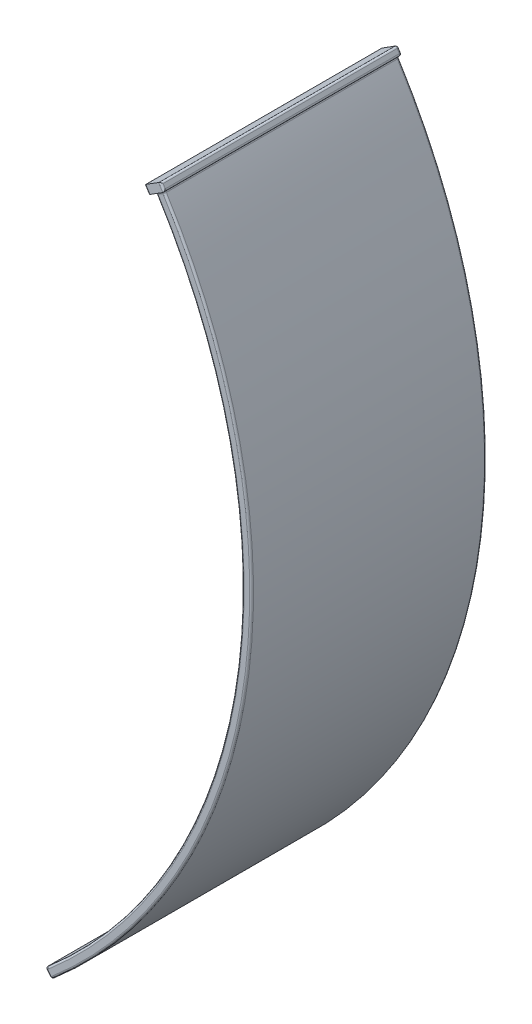
SolidWorks part; units mm, degrees
ref_plane "Front Plane" through (0, 0, 0) normal (0, 0, 1) x (1, 0, 0)
ref_plane "Top Plane" through (0, 0, 0) normal (0, 1, 0) x (1, 0, 0)
ref_plane "Right Plane" through (0, 0, 0) normal (1, 0, 0) x (0, 0, -1)
ref_plane "Plane1" through (-17.5, 0, 0) normal (1, 0, 0) x (0, 0, -1)
ref_plane "Plane2" through (-35, 0, 0) normal (1, 0, 0) x (0, 0, -1)
sketch "Sketch1" plane through (-17.5, 0, 0) normal (1, 0, 0) x (0, 0, -1)
  line L0 (0, 0) -> (0, -50) construction
  dimension "D1" = 50
sketch "Sketch2" plane through (0, 0, 0) normal (1, 0, 0) x (0, 0, -1)
  point P0 (0, 0)
sketch "Sketch3" plane through (-35, 0, 0) normal (1, 0, 0) x (0, 0, -1)
  point P0 (0, 0)
sketch "Sketch4" plane through (0, 0, 0) normal (0, 0, 1) x (1, 0, 0)
  line L0 (-17.5, 0) -> (-17.5, -50) construction
  arc A0 (9.9992, -0.126) -> (-45, -0.1273) centre (-17.5, -17.4818) cw construction
  arc A1 (9.9992, -0.126) -> (3.7287, -42.1146) centre (-17.5, -17.4818) cw construction
  dimension "D1" = 10
  dimension "D3" = 32.5182
  dimension "D4" = 46.2567
  dimension "D2" = 10
sketch "Sketch6" plane through (0, 0, 0) normal (0, 0, 1) x (1, 0, 0)
  line L0 (15.0182, 10) -> (15.0182, -39.6825) construction
  arc A0 (3.7287, -42.1146) -> (9.9992, -0.126) centre (-17.5, -17.4818) ccw construction
  dimension "D1" = 32.5182
ref_plane "Plane3" through (15.0182, 0, 0) normal (1, 0, 0) x (0, 0, -1)
sketch "Sketch7" plane through (0, 0, 0) normal (0, 0, 1) x (1, 0, 0)
  arc A0 (12.8322, 1.6619) -> (5.9157, -44.6523) centre (-17.5, -17.4818) cw
  dimension "D1" = 3.35
  dimension "D3" = 35.8682
  dimension "D2" = 3.35
sketch "Sketch8" plane through (0, 0, 0) normal (0, 0, 1) x (1, 0, 0)
  line L0 (18.3682, 1.0018) -> (18.3682, -40.6587) construction
  arc A0 (5.9157, -44.6523) -> (12.8322, 1.6619) centre (-17.5, -17.4818) ccw construction
ref_plane "Plane4" through (18.3682, 0, 0) normal (1, 0, 0) x (0, 0, -1)
sketch "Sketch10" plane through (18.3682, 0, 0) normal (1, 0, 0) x (0, 0, -1)
  line L0 (-26.4109, -17.4818) -> (24.946, -17.4818) construction
  dimension "D1" = 0
ref_plane "Plane5" through (0, -17.4818, 0) normal (0, 1, 0) x (1, 0, 0)
sketch "Sketch11" plane through (0, -17.4818, 0) normal (0, 1, 0) x (1, 0, 0)
  line L0 (18.3682, -26.4109) -> (18.3682, 24.946) construction
  line L1 (18.3682, 7.5) -> (18.9682, 7.5)
  line L2 (18.3682, 7.5) -> (18.3682, -7.5)
  line L3 (18.3682, -7.5) -> (18.9682, -7.5)
  line L4 (18.9682, 7.5) -> (18.9682, -7.5)
  line L5 (5.9157, 0) -> (18.3682, 0) construction
  dimension "D1" = 0.6
  dimension "D2" = 15
  dimension "D3" = 7.5
sweep "Sweep1" add profiles "Sketch11" path "Sketch7"
sketch "Sketch12" plane through (-18.687, -16.1046, 0) normal (-0.7575, -0.6528, 0) x (0, 0, 1)
  line L1 (-7.5, -37.6863) -> (7.5, -37.6863)
  line L2 (-7.5, -37.6863) -> (-7.5, -38.2863)
  line L3 (-7.5, -38.2863) -> (7.5, -38.2863)
  line L4 (7.5, -37.6863) -> (7.5, -38.2863)
extrude "Boss-Extrude1" add sketch "Sketch12" along normal blind 0.2
sketch "Sketch13" plane through (24.6026, -28.5477, 0) normal (-0.6528, 0.7575, 0) x (0.7575, 0.6528, 0)
  line L0 (-24.869, 0) -> (-24.669, 0) construction
  line L1 (-24.869, -7.5) -> (-24.869, 7.5) construction
  line L2 (-24.669, 7.5) -> (-24.669, -7.5) construction
  circle A0 centre (-23.369, 4) radius 0.55
  circle A1 centre (-23.369, -4) radius 0.55
  dimension "D1" = 1.1
  dimension "D2" = 1.5
  dimension "D3" = 4
extrude "Cut-Extrude1" cut sketch "Sketch13" against normal through all both and the other way through all
sketch "Sketch14" plane through (2.9053, -4.6033, 0) normal (-0.5337, 0.8457, 0) x (0.8457, 0.5337, 0)
  line L0 (12.3386, 7.5) -> (11.7386, 7.5) construction
  line L1 (12.6386, -7.7) -> (11.4386, -7.7)
  line L2 (12.6386, -7.7) -> (12.6386, 7.5)
  line L3 (12.6386, 7.5) -> (11.4386, 7.5)
  line L4 (11.4386, -7.7) -> (11.4386, 7.5)
  line L5 (12.3386, -7.5) -> (12.3386, 7.5) construction
  dimension "D1" = 1.2
  dimension "D2" = 15.2
  dimension "D3" = 0
  dimension "D4" = 0.3
extrude "Boss-Extrude2" add sketch "Sketch14" along normal blind 0.5
fillet "Fillet1" radius 0.12 30 edges at (5.7642, -44.7828, 0) (12.3116, 1.9246, 0.1) (12.445, 1.7132, 7.7) (12.5785, 1.5018, 0.1) (13.4598, 2.3537, 7.7) (13.3264, 2.5651, 0.1) (13.5932, 2.1423, 0.1) (5.8399, -44.7175, -7.5) (5.96, -45.0101, -7.5) (13.4664, 2.0622, -7.5) (13.4598, 2.3537, -7.5) (12.819, 2.2449, -7.5) (12.445, 1.7132, -7.5) (12.7053, 1.5819, -7.5) (5.96, -45.0101, 7.5) (5.8399, -44.7175, 7.5) (13.0859, 1.8221, 7.5) (6.2316, -45.172, -7.5) (6.1558, -45.2373, 0) (6.2316, -45.172, 7.5) (18.5682, -22.8682, 7.5) (13.3396, 1.9822, 0) (18.5682, -22.8682, -7.5) (7.6674, -43.8737, 4.1265) (7.6674, -43.8737, -3.8735) (17.9748, -22.7796, -7.5) (12.8322, 1.6619, 0) (17.9748, -22.7796, 7.5) (7.2752, -43.4186, 3.8735) (7.2752, -43.4186, -4.1265)
